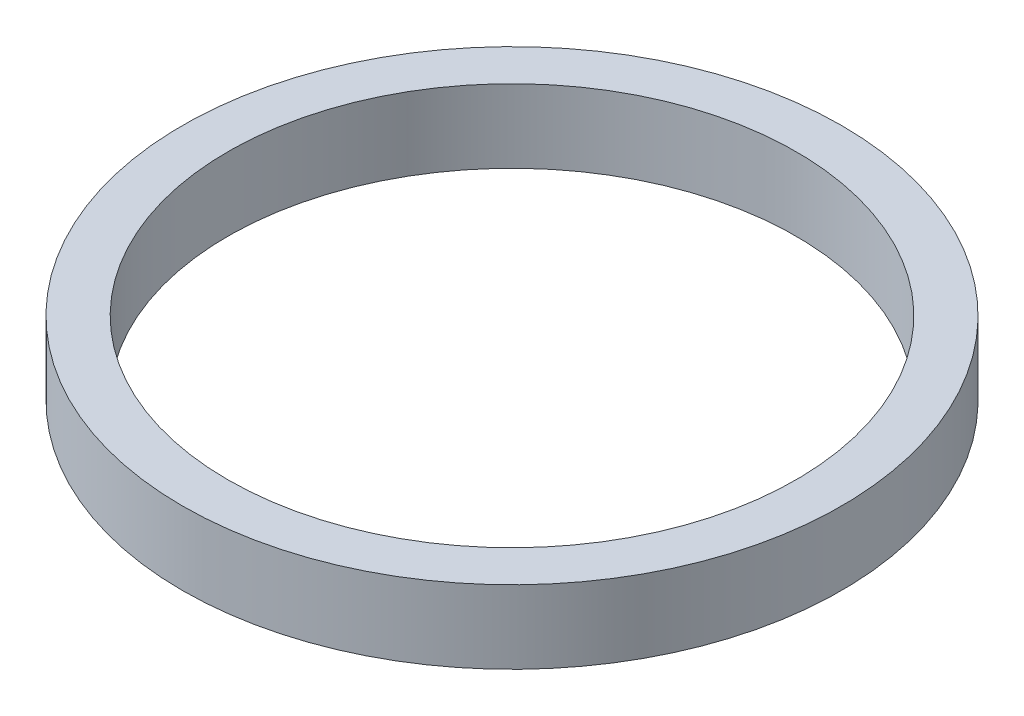
SolidWorks part; units mm, degrees
ref_plane "Front Plane" through (0, 0, 0) normal (0, 0, 1) x (1, 0, 0)
ref_plane "Top Plane" through (0, 0, 0) normal (0, 1, 0) x (1, 0, 0)
ref_plane "Right Plane" through (0, 0, 0) normal (1, 0, 0) x (0, 0, -1)
sketch "Sketch1" plane through (0, 0, 0) normal (0, 1, 0) x (1, 0, 0)
  circle A0 centre (0, 0) radius 57.15
  dimension "D1" = 114.3
extrude "Boss-Extrude1" add sketch "Sketch1" along normal blind 12.7
sketch "Sketch2" plane through (0, 12.7, 0) normal (0, 1, 0) x (1, 0, 0)
  circle A0 centre (0, 0) radius 49.276
  dimension "D1" = 98.552
extrude "Cut-Extrude1" cut sketch "Sketch2" against normal blind 12.7
